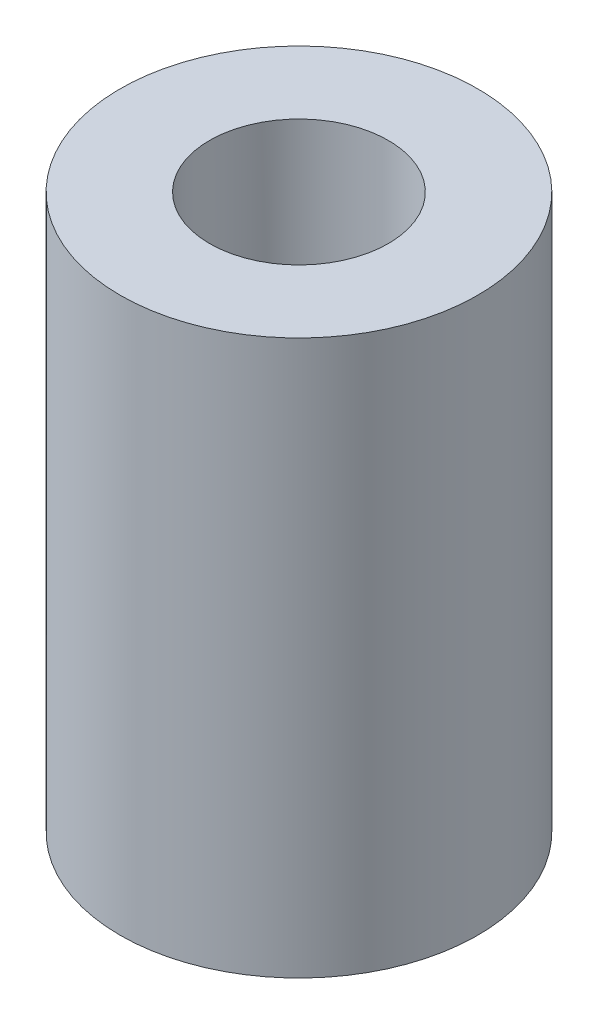
SolidWorks part; units mm, degrees
ref_plane "Front Plane" through (0, 0, 0) normal (0, 0, 1) x (1, 0, 0)
ref_plane "Top Plane" through (0, 0, 0) normal (0, 1, 0) x (1, 0, 0)
ref_plane "Right Plane" through (0, 0, 0) normal (1, 0, 0) x (0, 0, -1)
sketch "Sketch1" plane through (0, 0, 0) normal (0, 1, 0) x (1, 0, 0)
  circle A0 centre (0, 0) radius 5
  circle A1 centre (0, 0) radius 2.5
  dimension "D1" = 10
  dimension "D2" = 5
extrude "Boss-Extrude1" add sketch "Sketch1" along normal blind 15.5
sketch "Sketch2" plane through (0, 0, 0) normal (1, 0, 0) x (0, 0, -1)
  line L0 (2.5, 15.5) -> (-2.5, 15.5) construction
  line L1 (5, 0) -> (5, 15.5) construction
  circle A0 centre (0, 10.98) radius 1.5
  dimension "D1" = 4.52
  dimension "D3" = 3
  dimension "D2" = 5
extrude "Cut-Extrude1" cut sketch "Sketch2" against normal blind 15.5
